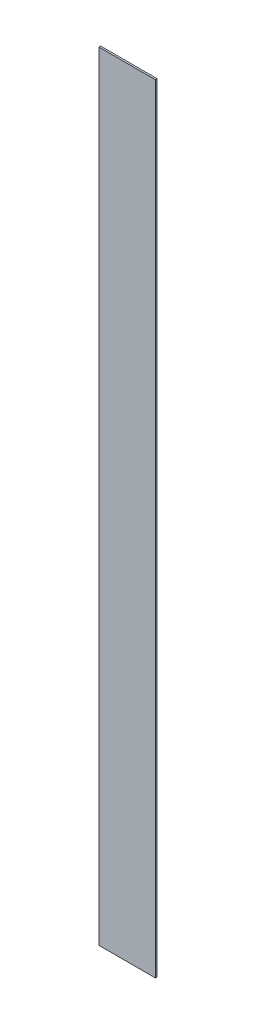
SolidWorks part; units mm, degrees
ref_plane "Front Plane" through (0, 0, 0) normal (0, 0, 1) x (1, 0, 0)
ref_plane "Top Plane" through (0, 0, 0) normal (0, 1, 0) x (1, 0, 0)
ref_plane "Right Plane" through (0, 0, 0) normal (1, 0, 0) x (0, 0, -1)
sketch "Sketch1" plane through (0, 0, 0) normal (0, 0, 1) x (1, 0, 0)
  line L1 (-12.7, -174.625) -> (12.7, -174.625)
  line L2 (-12.7, -174.625) -> (-12.7, 174.625)
  line L3 (-12.7, 174.625) -> (12.7, 174.625)
  line L4 (12.7, -174.625) -> (12.7, 174.625)
  line L5 (-12.7, -174.625) -> (12.7, 174.625) construction
  line L6 (-12.7, 174.625) -> (12.7, -174.625) construction
  point P0 (0, 0)
  dimension "D1" = 349.25
  dimension "D2" = 25.4
extrude "Boss-Extrude1" add sketch "Sketch1" along normal mid plane 0.7937
